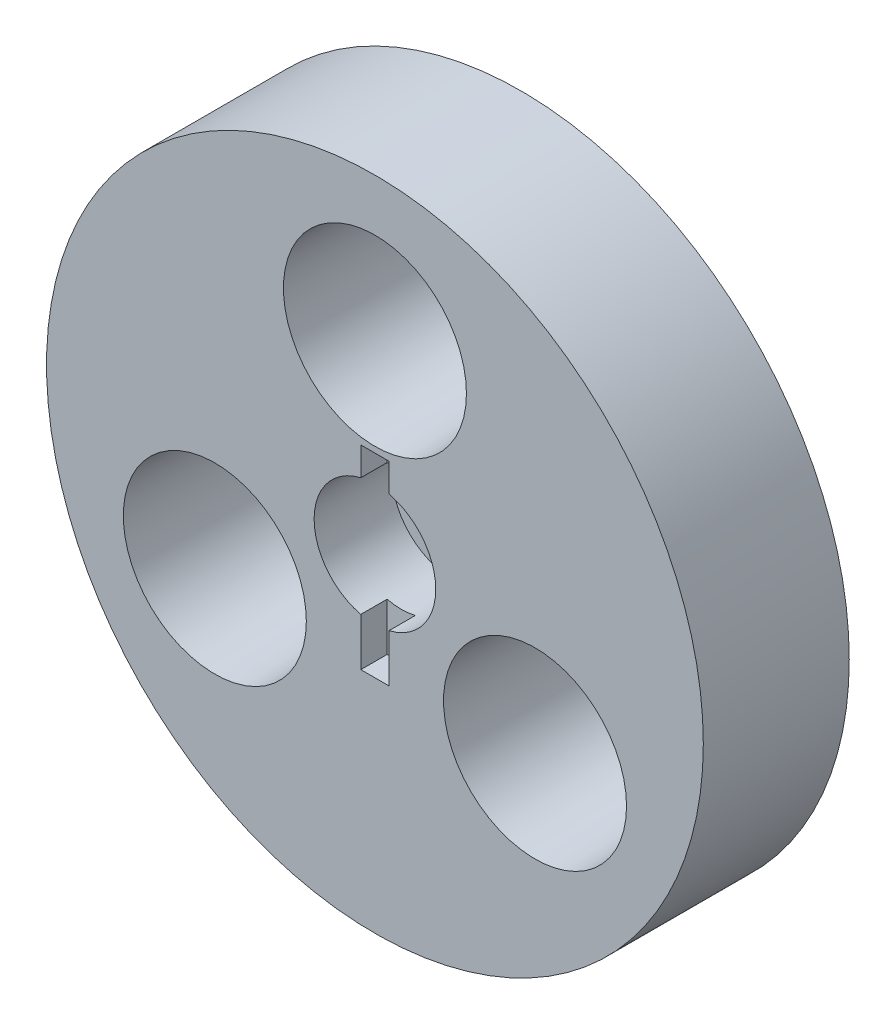
SolidWorks part; units mm, degrees
material "Teak"
ref_plane "Front Plane" through (0, 0, 0) normal (0, 0, 1) x (1, 0, 0)
ref_plane "Top Plane" through (0, 0, 0) normal (0, 1, 0) x (1, 0, 0)
ref_plane "Right Plane" through (0, 0, 0) normal (1, 0, 0) x (0, 0, -1)
sketch "Sketch1" plane through (0, 0, 0) normal (0, 0, 1) x (1, 0, 0)
  line L0 (0, 0) -> (20.8972, -12.065) construction
  line L1 (0, 42.8625) -> (0, -42.8625) construction
  line L2 (0, 0) -> (-20.8972, -12.065) construction
  line L3 (0, 24.13) -> (0, 0)
  circle A0 centre (0, 0) radius 42.8625
  circle A1 centre (0, 24.13) radius 11.1125
  circle A2 centre (-20.8972, -12.065) radius 11.1125
  circle A3 centre (20.8972, -12.065) radius 11.1125
  dimension "D3" = 85.725
  dimension "D5" = 22.225
  dimension "D1" = 120
  dimension "D2" = 120
  dimension "D4" = 24.13
extrude "Boss-Extrude1" add sketch "Sketch1" along normal mid plane 19.05
sketch "Sketch2" plane through (0, 0, 9.525) normal (0, 0, 1) x (1, 0, 0)
  circle A0 centre (0, 0) radius 7.9375
  dimension "D1" = 15.875
extrude "Cut-Extrude1" cut sketch "Sketch2" against normal blind 10.16
sketch "Sketch3" plane through (0, 0, 9.525) normal (0, 0, 1) x (1, 0, 0)
  line L0 (0, 11.43) -> (0, -13.97) construction
  line L1 (1.8415, 11.43) -> (-1.8415, 11.43)
  line L2 (1.8415, 11.43) -> (1.8415, -13.97)
  line L3 (1.8415, -13.97) -> (-1.8415, -13.97)
  line L4 (-1.8415, 11.43) -> (-1.8415, -13.97)
  circle A0 centre (0, 24.13) radius 11.1125 construction
  dimension "D1" = 3.683
  dimension "D2" = 25.4
  dimension "D3" = 12.7
extrude "Cut-Extrude2" cut sketch "Sketch3" against normal blind 3.429
draft "Draft2" type of draft neutral plane draft angle 2.5 faces to draft 3 face at (-9.7847, -12.065, 9.525) face at (32.0097, -12.065, 9.525) face at (11.1125, 24.13, 9.525) neutral plane through (0, 0, -9.525) neutral plane normal (0, 0, -1) reverse direction yes parameters "D1"=2.5
